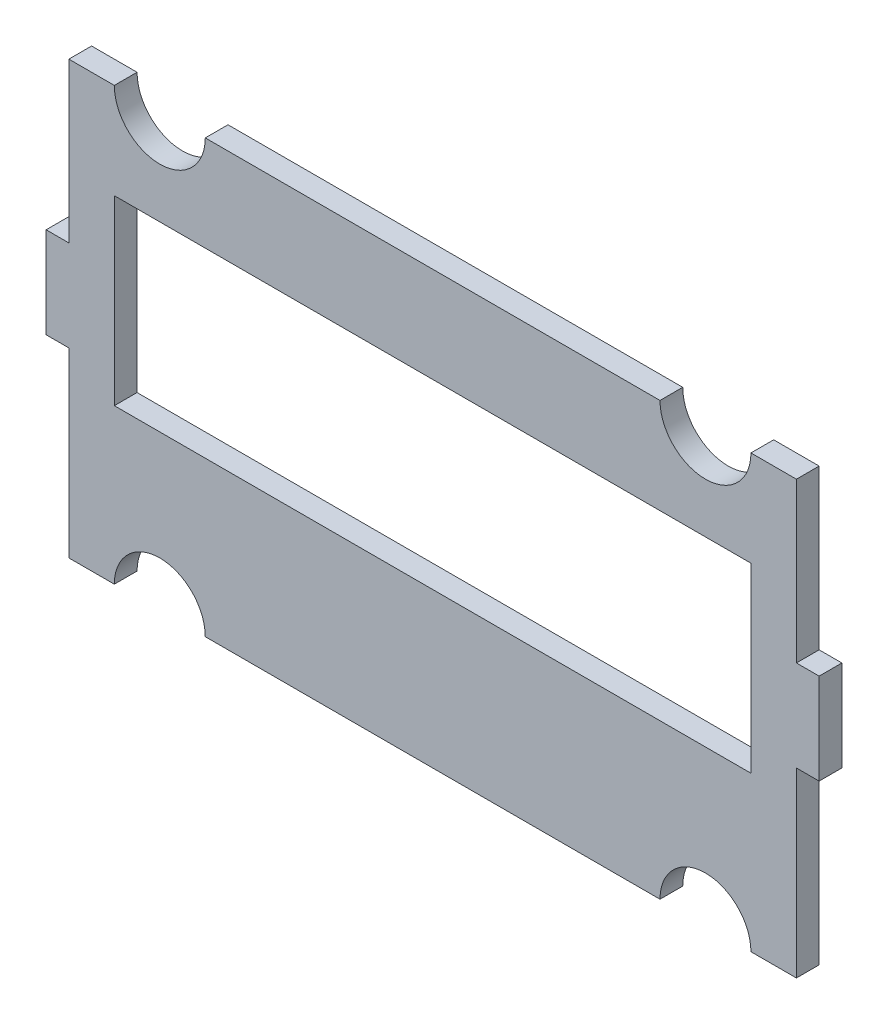
SolidWorks part; units mm, degrees
ref_plane "Front Plane" through (0, 0, 0) normal (0, 0, 1) x (1, 0, 0)
ref_plane "Top Plane" through (0, 0, 0) normal (0, 1, 0) x (1, 0, 0)
ref_plane "Right Plane" through (0, 0, 0) normal (1, 0, 0) x (0, 0, -1)
sketch "Sketch1" plane through (0, 0, 0) normal (0, 0, 1) x (1, 0, 0)
  line L1 (0, 0) -> (101.6, 0)
  line L2 (0, 0) -> (0, 63.5)
  line L3 (0, 63.5) -> (101.6, 63.5)
  line L4 (101.6, 0) -> (101.6, 63.5)
  dimension "D1" = 63.5
  dimension "D2" = 101.6
extrude "Boss-Extrude1" add sketch "Sketch1" along normal blind 3.175
sketch "Sketch2" plane through (0, 0, 3.175) normal (0, 0, 1) x (1, 0, 0)
  line L1 (6.35, 46.99) -> (95.25, 46.99)
  line L2 (6.35, 46.99) -> (6.35, 21.59)
  line L3 (6.35, 21.59) -> (95.25, 21.59)
  line L4 (95.25, 46.99) -> (95.25, 21.59)
  line L5 (0, 63.5) -> (0, 0) construction
  line L8 (0, 0) -> (101.6, 0) construction
  dimension "D1" = 21.59
  dimension "D2" = 88.9
  dimension "D3" = 25.4
  dimension "D4" = 6.35
extrude "Cut-Extrude1" cut sketch "Sketch2" against normal through all
sketch "Sketch3" plane through (0, 0, 3.175) normal (0, 0, 1) x (1, 0, 0)
  line L0 (0, 63.5) -> (0, 0) construction
  line L1 (0, 38.1) -> (-3.175, 38.1)
  line L2 (0, 38.1) -> (0, 25.4)
  line L3 (0, 25.4) -> (-3.175, 25.4)
  line L4 (-3.175, 38.1) -> (-3.175, 25.4)
  line L5 (50.8, 63.5) -> (50.8, 0) construction
  line L6 (101.6, 63.5) -> (0, 63.5) construction
  line L7 (0, 0) -> (101.6, 0) construction
  line L8 (101.6, 25.4) -> (104.775, 25.4)
  line L9 (101.6, 38.1) -> (101.6, 25.4)
  line L10 (101.6, 38.1) -> (104.775, 38.1)
  line L11 (104.775, 38.1) -> (104.775, 25.4)
  point P12 (0, 31.75)
  point P13 (0, 31.75)
  dimension "D1" = 12.7
  dimension "D2" = 3.175
extrude "Boss-Extrude2" add sketch "Sketch3" against normal up to surface (3.175 mm away) up to face at (50.8, 34.29, 0)
sketch "Sketch4" plane through (0, 0, 3.175) normal (0, 0, 1) x (1, 0, 0)
  line L0 (101.6, 38.1) -> (101.6, 63.5) construction
  line L1 (0, 63.5) -> (101.6, 63.5)
  line L2 (0, 63.5) -> (0, 60.325)
  line L3 (0, 60.325) -> (101.6, 60.325)
  line L4 (101.6, 63.5) -> (101.6, 60.325)
  dimension "D1" = 3.175
extrude "Cut-Extrude2" cut sketch "Sketch4" against normal through all
sketch "Sketch7" plane through (0, 0, 3.175) normal (0, 0, 1) x (1, 0, 0)
  line L0 (0, 0) -> (101.6, 0) construction
  line L1 (50.8, 60.325) -> (50.8, 0) construction
  line L2 (0, 60.325) -> (101.6, 60.325) construction
  line L3 (-3.175, 31.75) -> (104.775, 31.75) construction
  line L4 (-3.175, 38.1) -> (-3.175, 25.4) construction
  line L5 (104.775, 25.4) -> (104.775, 38.1) construction
  line L6 (6.35, 0) -> (19.05, 0)
  line L7 (0, 25.4) -> (0, 0) construction
  line L8 (95.25, 0) -> (82.55, 0)
  line L9 (6.35, 60.325) -> (19.05, 60.325)
  line L10 (95.25, 60.325) -> (82.55, 60.325)
  arc A0 (19.05, 0) -> (6.35, 0) centre (12.7, 0) ccw
  arc A1 (82.55, 0) -> (95.25, 0) centre (88.9, 0) cw
  arc A2 (6.35, 60.325) -> (19.05, 60.325) centre (12.7, 60.325) ccw
  arc A3 (95.25, 60.325) -> (82.55, 60.325) centre (88.9, 60.325) cw
  point P21 (0, 0)
  dimension "D1" = 6.35
  dimension "D3" = 12.7
  dimension "D2" = 12.7
extrude "Cut-Extrude5" cut sketch "Sketch7" against normal through all
